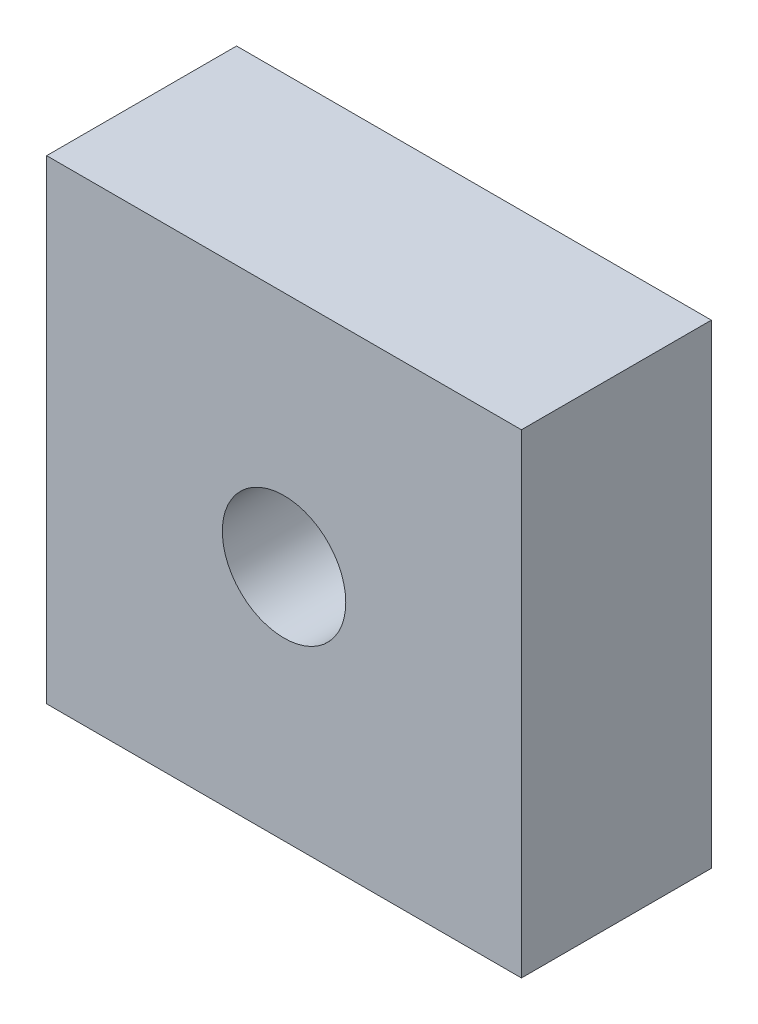
SolidWorks part; units mm, degrees
ref_plane "Front Plane" through (0, 0, 0) normal (0, 0, 1) x (1, 0, 0)
ref_plane "Top Plane" through (0, 0, 0) normal (0, 1, 0) x (1, 0, 0)
ref_plane "Right Plane" through (0, 0, 0) normal (1, 0, 0) x (0, 0, -1)
sketch "Sketch1" plane through (0, 0, 0) normal (0, 0, 1) x (1, 0, 0)
  line L0 (7.5, 7.5) -> (7.5, 15) construction
  line L1 (0, 0) -> (15, 0)
  line L2 (0, 0) -> (0, 15)
  line L3 (0, 15) -> (15, 15)
  line L4 (15, 0) -> (15, 15)
  line L5 (7.5, 7.5) -> (15, 7.5) construction
  circle A0 centre (7.5, 7.5) radius 1.95
  dimension "D3" = 3.9
  dimension "D1" = 15
  dimension "D2" = 15
extrude "Boss-Extrude1" add sketch "Sketch1" along normal blind 6
